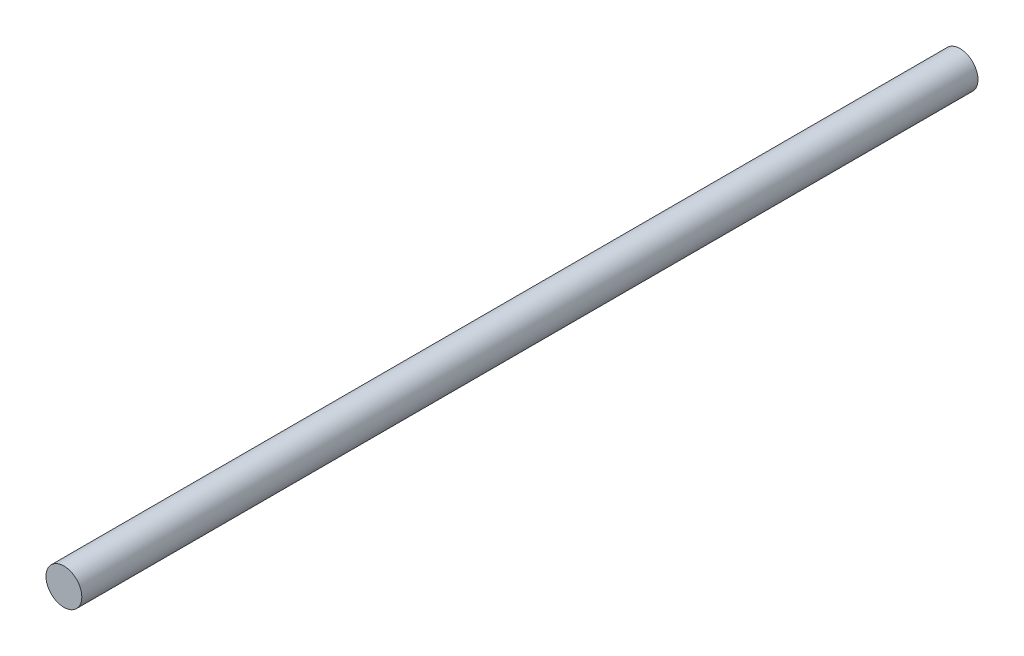
SolidWorks part; units mm, degrees
ref_plane "Alzado" through (0, 0, 0) normal (0, 0, 1) x (1, 0, 0)
ref_plane "Planta" through (0, 0, 0) normal (0, 1, 0) x (1, 0, 0)
ref_plane "Vista lateral" through (0, 0, 0) normal (1, 0, 0) x (0, 0, -1)
sketch "Croquis1" plane through (0, 0, 0) normal (0, 0, 1) x (1, 0, 0)
  circle A0 centre (0, 0) radius 4
  dimension "D1" = 8
extrude "Saliente-Extruir1" add sketch "Croquis1" along normal blind 200
